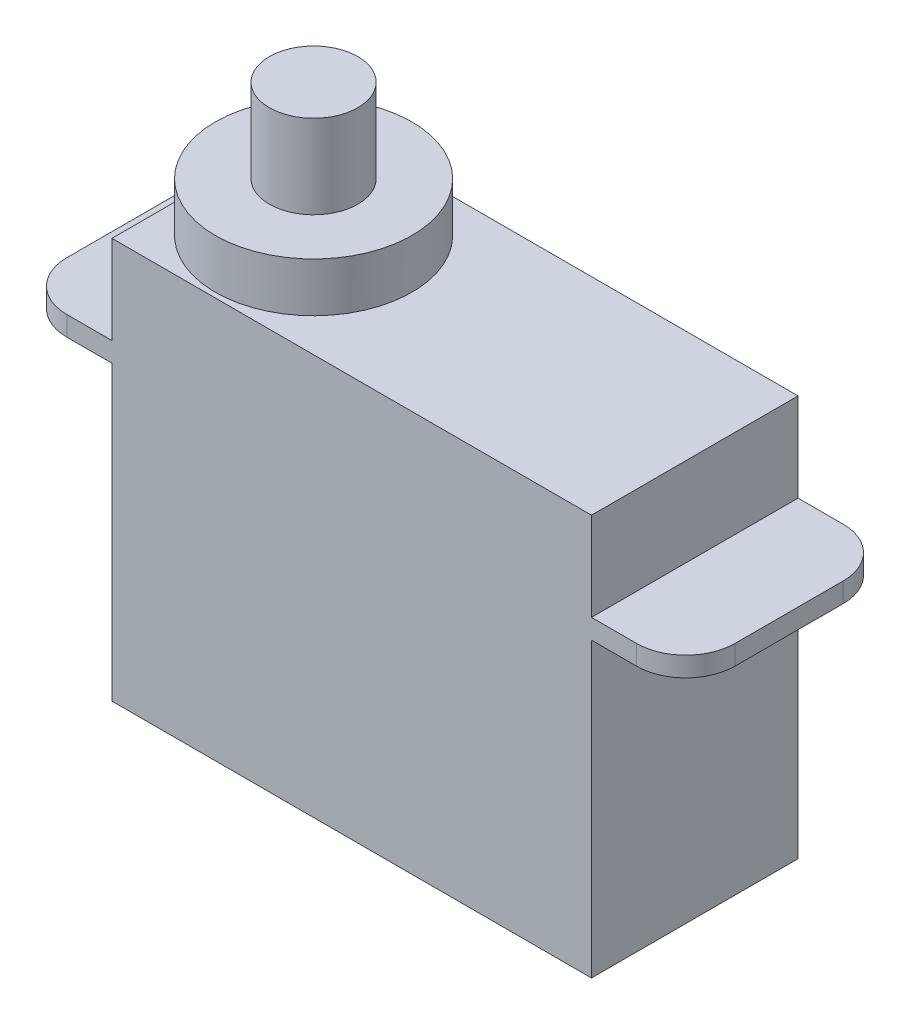
SolidWorks part; units mm, degrees
ref_plane "Front Plane" through (0, 0, 0) normal (0, 0, 1) x (1, 0, 0)
ref_plane "Top Plane" through (0, 0, 0) normal (0, 1, 0) x (1, 0, 0)
ref_plane "Right Plane" through (0, 0, 0) normal (1, 0, 0) x (0, 0, -1)
sketch "Sketch1" plane through (0, 0, 0) normal (0, 1, 0) x (1, 0, 0)
  line L1 (0, 0) -> (19.5, 0)
  line L2 (0, 0) -> (0, 8.4)
  line L3 (0, 8.4) -> (19.5, 8.4)
  line L4 (19.5, 0) -> (19.5, 8.4)
  dimension "D1" = 8.4
  dimension "D2" = 19.5
extrude "Boss-Extrude1" add sketch "Sketch1" along normal blind 16.3
sketch "Sketch2" plane through (0, 16.3, 0) normal (0, 1, 0) x (1, 0, 0)
  line L0 (0, 0) -> (0, 8.4) construction
  line L1 (0, 4.2) -> (19.5, 4.2) construction
  line L2 (19.5, 0) -> (19.5, 8.4) construction
  circle A0 centre (4, 4.2) radius 4
  point P10 (0, 0)
  point P11 (0, 0)
  dimension "D1" = 8
extrude "Boss-Extrude2" add sketch "Sketch2" along normal blind 2
sketch "Sketch3" plane through (19.5, 0, 0) normal (1, 0, 0) x (0, 0, -1)
  line L0 (0, 12.7) -> (8.4, 12.7)
  line L1 (0, 16.3) -> (0, 0) construction
  line L2 (8.4, 16.3) -> (8.4, 0) construction
  line L3 (0, 0) -> (8.4, 0) construction
  line L4 (0, 12.7) -> (0, 11.9)
  line L5 (0, 11.9) -> (8.4, 11.9)
  line L6 (8.4, 11.9) -> (8.4, 12.7)
  dimension "D1" = 12.7
  dimension "D2" = 0.8
extrude "Boss-Extrude3" add sketch "Sketch3" along normal blind 3.835
fillet "Fillet1" radius 2 2 edges at (23.335, 12.3, -8.4) (23.335, 12.3, 0)
ref_plane "Plane1" through (9.75, 0, 0) normal (1, 0, 0) x (0, 0, -1)
mirror "Mirror1" about plane through (9.75, 0, 0) normal (1, 0, 0) of "Boss-Extrude3"
fillet "Fillet2" radius 2 2 edges at (-3.835, 12.3, 0) (-3.835, 12.3, -8.4)
sketch "Sketch4" plane through (0, 18.3, 0) normal (0, 1, 0) x (1, 0, 0)
  circle A0 centre (4, 4.2) radius 1.8
  dimension "D1" = 3.6
extrude "Boss-Extrude4" add sketch "Sketch4" along normal blind 3.4
